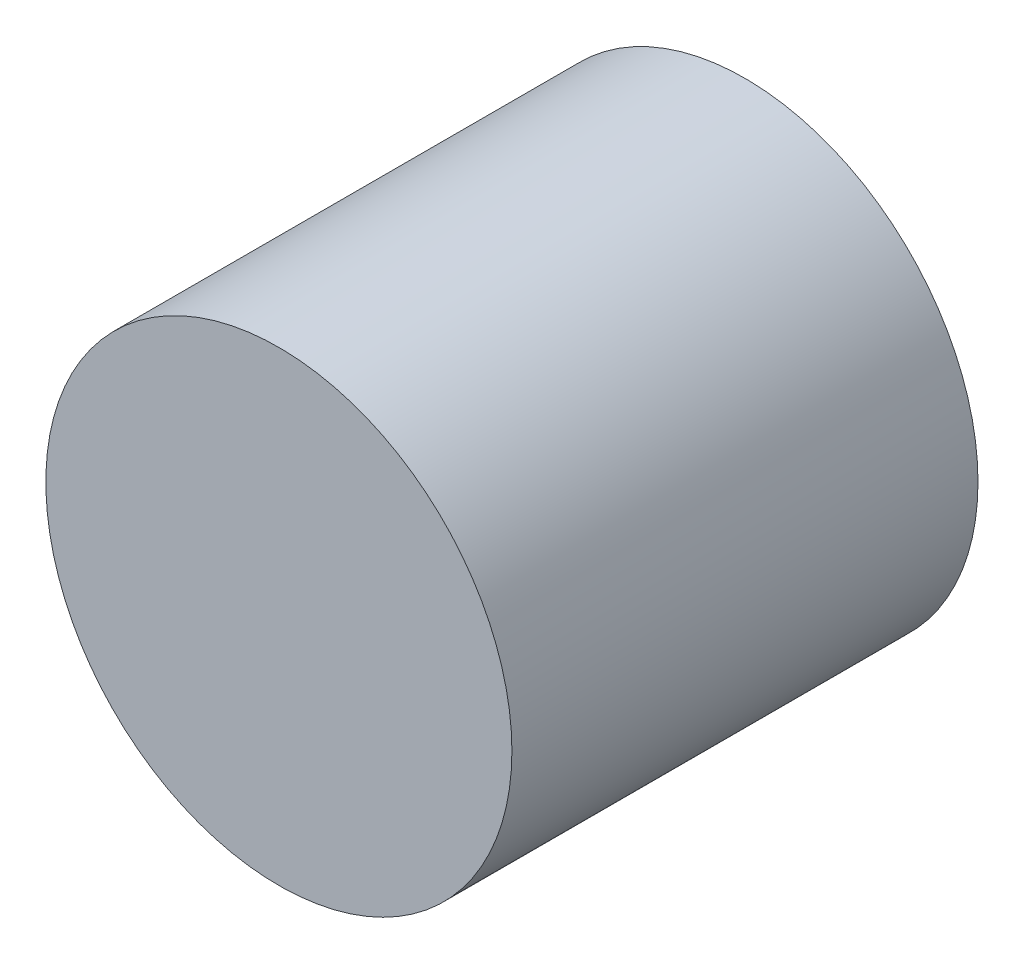
SolidWorks part; units mm, degrees
ref_plane "Ön Düzlem" through (0, 0, 0) normal (0, 0, 1) x (1, 0, 0)
ref_plane "Üst Düzlem" through (0, 0, 0) normal (0, 1, 0) x (1, 0, 0)
ref_plane "Sağ Düzlem" through (0, 0, 0) normal (1, 0, 0) x (0, 0, -1)
sketch "Çizim1" plane through (0, 0, 0) normal (0, 0, 1) x (1, 0, 0)
  circle A0 centre (0, 0) radius 3.5
  dimension "D1" = 7
extrude "Yükseklik-Ekstrüzyon1" add sketch "Çizim1" along normal blind 7
